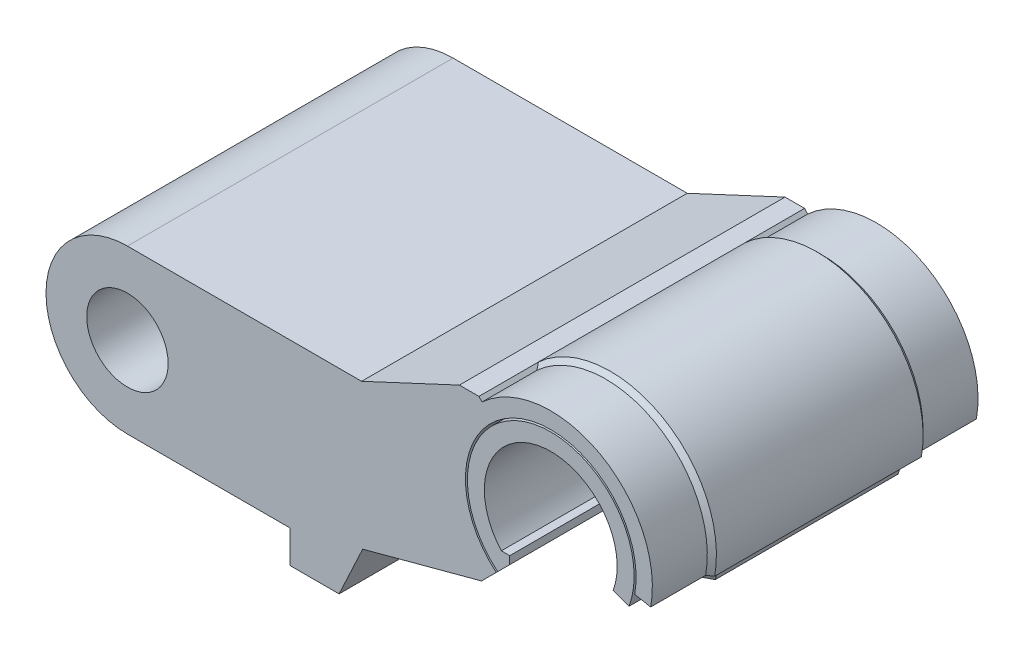
SolidWorks part; units mm, degrees
ref_plane "Front Plane" through (0, 0, 0) normal (0, 0, 1) x (1, 0, 0)
ref_plane "Top Plane" through (0, 0, 0) normal (0, 1, 0) x (1, 0, 0)
ref_plane "Right Plane" through (0, 0, 0) normal (1, 0, 0) x (0, 0, -1)
sketch "Sketch9" plane through (0, 0, 0) normal (0, 0, 1) x (1, 0, 0)
  line L0 (0, 0) -> (-40, 0) construction
  line L1 (-40, 0) -> (-40, -20) construction
  dimension "D1" = 20
  dimension "D2" = 40
sketch "Sketch1" plane through (0, 0, 0) normal (0, 0, 1) x (1, 0, 0)
  line L0 (7.5, -6.6144) -> (-7.5, -6.6144) construction
  line L1 (-7.5, -6.6144) -> (-6.3, -6.6144)
  line L2 (-6.3, -6.6144) -> (-6.3, 1.2617)
  line L3 (-6.3, 1.2617) -> (0, 4.899) construction
  line L4 (5, 4.899) -> (-5, 4.899) construction
  line L5 (0, -14.4444) -> (0, 14.4444) construction
  line L6 (-5.5, 5.199) -> (5.5, 5.199)
  line L7 (-6.3, 1.2617) -> (-3.7026, 2.7613)
  line L8 (0, 0) -> (-7.1429, 6.9985) construction
  line L9 (-5.5, 4.399) -> (-3.7026, 3.3613)
  line L10 (-5.5, 5.199) -> (-5.5, 4.399)
  line L11 (-3.7026, 3.3613) -> (-3.7026, 2.7613)
  line L12 (7.5, -6.6144) -> (6.3, -6.6144)
  line L13 (3.7026, 3.3613) -> (3.7026, 2.7613)
  line L14 (5.5, 5.199) -> (5.5, 4.399)
  line L15 (5.5, 4.399) -> (3.7026, 3.3613)
  line L16 (6.3, 1.2617) -> (3.7026, 2.7613)
  line L17 (6.3, -6.6144) -> (6.3, 1.2617)
  circle A0 centre (0, 0) radius 10 construction
  arc A1 (-7.5, -6.6144) -> (7.5, -6.6144) centre (0, 0) cw
  point P11 (0, 4.899)
  point P14 (0, 0)
sketch "Sketch2" plane through (0, 0, 0) normal (-1, 0, 0) x (0, 0, 1)
  line L0 (0, 10) -> (0, 15)
  line L3 (0, 15) -> (-3, 15)
  line L4 (-3, 15) -> (-9, 9)
  line L5 (-9, 9) -> (0, 9)
  line L6 (0, 9) -> (0, 10)
sketch "Sketch11" plane through (-40, -20, 0) normal (0, 0, -1) x (-1, 0, 0)
  line L0 (0, 0) -> (0, -150.5823)
  line L1 (0, 0) -> (15, 0)
  line L2 (15, 0) -> (43.25, -60.5823)
  line L3 (43.25, -60.5823) -> (53.25, -60.5823)
  line L4 (53.25, -60.5823) -> (53.25, -150.5823)
  line L5 (53.25, -150.5823) -> (72.25, -150.5823)
  line L6 (91.25, -150.5823) -> (91.25, -10.5823)
  line L7 (91.25, -10.5823) -> (114.25, -10.5823)
  line L8 (114.25, -10.5823) -> (114.25, -150.5823)
  line L9 (72.25, -150.5823) -> (91.25, -150.5823)
sketch "Sketch3" plane through (0, 0, 0) normal (0, 0, 1) x (1, 0, 0)
  line L0 (0, 15) -> (0, 15.2) construction
  line L1 (6.3, -8.0144) -> (9.8566, -11.571)
  line L2 (6.3, -6.8144) -> (6.3, -8.0144)
  line L16 (-6.3, -6.8144) -> (-6.3, -8.0144)
  line L17 (-6.3, -8.0144) -> (-9.8566, -11.571)
  line L18 (6.3, -6.8144) -> (7.5897, -6.8144)
  line L19 (-7.5897, -6.8144) -> (-6.3, -6.8144)
  line L20 (6.3, -6.8144) -> (7.5897, -6.8144)
  line L21 (-7.5897, -6.8144) -> (-6.3, -6.8144)
  arc A4 (-9.8566, -11.571) -> (9.8566, -11.571) centre (0, 0) cw
  arc A5 (7.5897, -6.8144) -> (-7.5897, -6.8144) centre (0, 0) ccw
  arc A6 (7.5897, -6.8144) -> (-7.5897, -6.8144) centre (0, 0) ccw
  dimension "D3" = 45
  dimension "D2" = 0.2
  dimension "D4" = 1.2
  dimension "D1" = 0.2
extrude "Boss-Extrude1" add sketch "Sketch3" along normal mid plane 50
sketch "Sketch4" plane through (0, 0, 0) normal (1, 0, 0) x (0, 0, -1)
  line L0 (0, 15) -> (0, 15.2) construction
  line L4 (-3.0828, 15.2) -> (-9.4828, 8.8)
  line L7 (9.4828, 8.8) -> (0, 8.8)
  line L8 (3.0828, 15.2) -> (9.4828, 8.8)
  line L9 (0, 15.2) -> (3.0828, 15.2)
  line L10 (9.4828, 8.8) -> (-9.4828, 8.8)
  line L11 (3.0828, 15.2) -> (9.4828, 8.8)
  line L12 (-3.0828, 15.2) -> (3.0828, 15.2)
  dimension "D1" = 0.2
extrude "Cut-Extrude1" cut sketch "Sketch4" against normal mid plane 5.2
sketch "Sketch5" plane through (0, 0, 0) normal (1, 0, 0) x (0, 0, -1)
  line L0 (-25, 15.2) -> (-3.0828, 15.2)
  line L4 (3.0828, 15.2) -> (25, 15.2)
  line L5 (3.0828, 15.2) -> (25, 15.2) construction
  line L6 (25, 15.2) -> (25, 12.8)
  line L7 (25, 12.8) -> (16.4414, 12.8)
  line L8 (16.4414, 12.8) -> (14.0414, 15.2)
  line L9 (14.0414, 15.2) -> (25, 15.2)
  line L10 (25, 15.2) -> (3.0828, 15.2) construction
  line L11 (-27.2236, 0) -> (27.2236, 0) construction
  point P18 (0, 0)
  dimension "D1" = 45
  dimension "D2" = 2.4
revolve "Cut-Revolve1" cut sketch "Sketch5" angle 360 about L11
mirror "Mirror1" about plane through (0, 0, 0) normal (0, 0, 1) of "Cut-Revolve1"
sketch "Sketch7" plane through (0, 0, 0) normal (1, 0, 0) x (0, 0, -1)
  line L0 (16.4414, 12.8) -> (14.0414, 15.2)
  line L1 (16.4414, 12.8) -> (14.0414, 15.2) construction
  line L2 (25, 12.8) -> (16.4414, 12.8)
  line L3 (25, 12.8) -> (16.4414, 12.8) construction
  line L9 (-29.9525, 0) -> (29.9525, 0) construction
  line L10 (0, 0) -> (0, 27.8077) construction
  line L11 (-14.0414, 15.2) -> (-3.0828, 15.2)
  line L12 (3.0828, 15.2) -> (14.0414, 15.2)
  line L13 (3.0828, 15.2) -> (14.0414, 15.2) construction
  line L14 (25, 13.1) -> (16.5657, 13.1)
  line L15 (16.5657, 13.1) -> (14.1657, 15.5)
  line L16 (3.0828, 15.5) -> (14.1657, 15.5)
  line L17 (3.0828, 15.5) -> (-3.0828, 15.5)
  line L18 (-3.0828, 15.5) -> (-14.1657, 15.5)
  line L19 (-16.5657, 13.1) -> (-14.1657, 15.5)
  line L20 (-25, 13.1) -> (-16.5657, 13.1)
  line L22 (25, 13.1) -> (25, 15.6)
  line L23 (25, 15.6) -> (16.5657, 15.6)
  line L24 (16.5657, 15.6) -> (15.8657, 16.3)
  line L25 (15.8657, 16.3) -> (-15.8657, 16.3)
  line L26 (-3.0828, 15.2) -> (-14.0414, 15.2) construction
  line L27 (-16.4414, 12.8) -> (-14.0414, 15.2) construction
  line L28 (-16.5657, 15.6) -> (-15.8657, 16.3)
  line L29 (-25, 15.6) -> (-16.5657, 15.6)
  line L30 (-25, 13.1) -> (-25, 15.6)
  point P12 (0, 0)
  point P22 (0, 15.5)
  point P26 (0, 25)
  point P32 (0, 16.3)
  dimension "D2" = 0.8
  dimension "D3" = 2.5
  dimension "D1" = 0.3
revolve "Revolve1" add sketch "Sketch7" angle 360 about L9
sketch "Sketch10" plane through (0, 0, 0) normal (0, 0, 1) x (1, 0, 0)
  line L0 (-6.3, -8.0144) -> (-9.8566, -11.571)
  line L1 (-6.3, -8.0144) -> (-9.8566, -11.571)
  line L2 (-9.8566, -11.571) -> (-28.2856, -30)
  line L5 (0, -14.4444) -> (0, 14.4444) construction
  line L6 (0, 0) -> (0, -30) construction
  line L9 (-6.3, -8.0144) -> (0, 0)
  line L10 (-28.2856, -30) -> (0, -30)
  line L11 (0, 0) -> (29.5047, -5.4288)
  line L12 (-9.8566, -11.571) -> (0, 0) construction
  arc A0 (29.5047, -5.4288) -> (0, -30) centre (0, 0) cw
  dimension "D1" = 120
  dimension "D2" = 30
extrude "Cut-Extrude2" cut sketch "Sketch10" against normal through all both and the other way through all
sketch "Sketch12" plane through (0, 0, 0) normal (0, 0, 1) x (1, 0, 0)
  line L0 (-40, -20) -> (-40, -25)
  line L1 (-40, -20) -> (-40, -170.5823) construction
  line L2 (-40, -25) -> (-32.5, -25)
  line L3 (-32.5, -25) -> (-28.8813, -17.2397)
  line L4 (-28.8813, -17.2397) -> (-10.6367, -12.3511)
  line L5 (-10.0694, -11.7838) -> (-10.6367, -12.3511)
  line L6 (-10.0694, -11.7838) -> (-10.6367, -12.3511) construction
  line L7 (-40, -20) -> (-65, -20)
  line L8 (-29.0429, 5) -> (-65, 5)
  line L9 (-65, 5) -> (-65, -20) construction
  line L10 (-11.0313, 12) -> (-14.0313, 12)
  line L11 (-14.0313, 12) -> (-29.0429, 5)
  arc A0 (16.0309, -2.9496) -> (-10.6367, -12.3511) centre (0, 0) ccw
  arc A1 (16.0309, -2.9496) -> (-10.6367, -12.3511) centre (0, 0) ccw construction
  arc A2 (-65, 5) -> (-65, -20) centre (-65, -7.5) ccw
  arc A3 (-11.0313, 12) -> (-10.6367, -12.3511) centre (0, 0) ccw
  dimension "D1" = 5
  dimension "D2" = 7.5
  dimension "D3" = 115
  dimension "D4" = 130
  dimension "D5" = 10
  dimension "D6" = 25
  dimension "D7" = 3
  dimension "D8" = 25
  dimension "D9" = 7
extrude "Boss-Extrude2" add sketch "Sketch12" along normal mid plane 50
sketch "Sketch13" plane through (0, 0, -25) normal (0, 0, -1) x (-1, 0, 0)
  line L0 (11.0313, 12) -> (10.5576, 11.4847)
  line L1 (10.1403, -11.8547) -> (10.6367, -12.3511)
  line L2 (-15.3425, -2.823) -> (-12.8837, -2.3706)
  line L3 (8.3662, -10.0805) -> (10.1403, -11.8547)
  line L8 (40, -20) -> (65, -20)
  line L9 (65, 5) -> (29.0429, 5)
  line L10 (29.0429, 5) -> (14.0313, 12)
  line L11 (14.0313, 12) -> (11.0313, 12)
  line L12 (10.6367, -12.3511) -> (28.8813, -17.2397)
  line L13 (28.8813, -17.2397) -> (32.5, -25)
  line L14 (32.5, -25) -> (40, -25)
  line L15 (40, -25) -> (40, -20)
  arc A0 (10.1403, -11.8547) -> (10.5576, 11.4847) centre (0, 0) ccw
  arc A2 (65, -20) -> (65, 5) centre (65, -7.5) ccw
  arc A3 (10.6367, -12.3511) -> (11.0313, 12) centre (0, 0) ccw
  arc A5 (10.6367, -12.3511) -> (11.0313, 12) centre (0, 0) ccw
  arc A6 (10.1403, -11.8547) -> (-15.3425, -2.823) centre (0, 0) ccw
  arc A7 (8.3662, -10.0805) -> (-12.8837, -2.3706) centre (0, 0) ccw
  arc A8 (10.1403, -11.8547) -> (-15.3425, -2.823) centre (0, 0) ccw construction
  dimension "D1" = 0
  dimension "D2" = 0
extrude "Boss-Extrude3" add sketch "Sketch13" against normal up to vertex
mirror "Mirror2" about plane through (0, 0, 0) normal (0, 0, 1) of "Boss-Extrude3"
sketch "Sketch15" plane through (0, 0, 0) normal (0, 0, 1) x (1, 0, 0)
  arc A0 (-65, 5) -> (-65, -20) centre (-65, -7.5) ccw
  arc A1 (-65, 5) -> (-65, -20) centre (-65, -7.5) ccw construction
  circle A2 centre (-65, -7.5) radius 6.25
  dimension "D1" = 12.5
extrude "Cut-Extrude3" cut sketch "Sketch15" against normal through all both and the other way through all
sketch "Sketch16" plane through (0, 0, 0) normal (0, 0, 1) x (1, 0, 0)
  line L0 (0, 0) -> (14.2833, -5.1987)
  line L1 (0, -15.2) -> (0, 0)
  arc A0 (9.8566, -11.571) -> (-9.8566, -11.571) centre (0, 0) ccw construction
  arc A1 (14.2833, -5.1987) -> (0, -15.2) centre (0, 0) cw
  dimension "D1" = 70
extrude "Cut-Extrude4" cut sketch "Sketch16" against normal through all both and the other way through all
